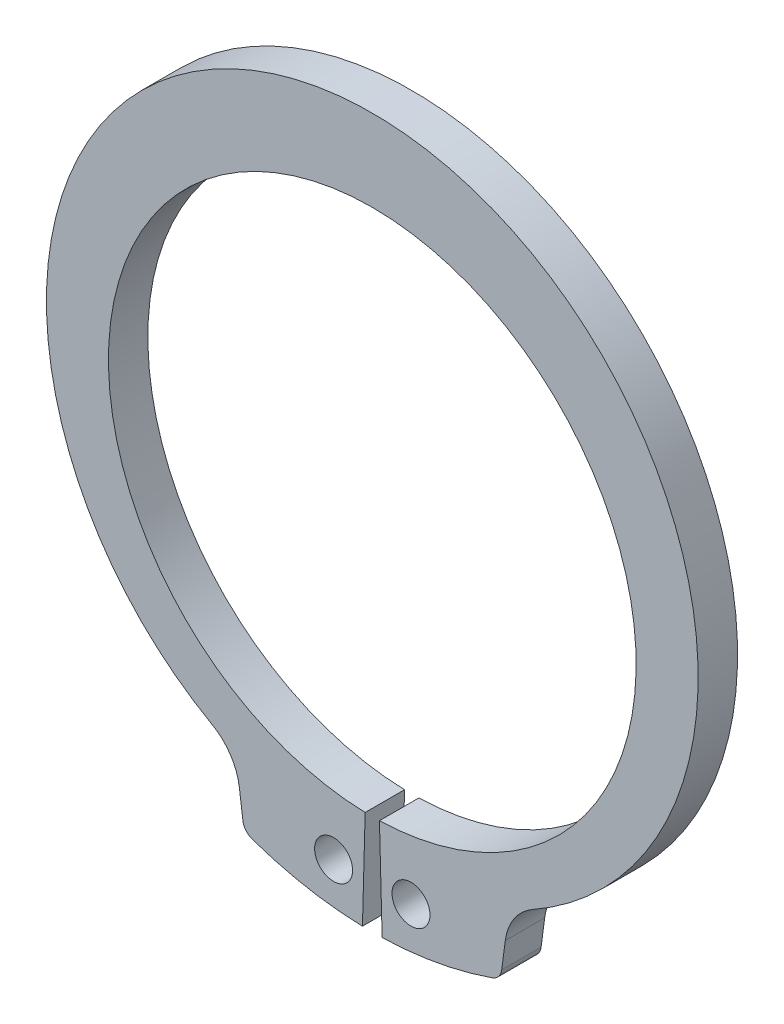
SolidWorks part; units mm, degrees
ref_plane "Plane1" through (0, 0, 0) normal (0, 0, 1) x (1, 0, 0)
ref_plane "Plane2" through (0, 0, 0) normal (0, 1, 0) x (1, 0, 0)
ref_plane "Plane3" through (0, 0, 0) normal (1, 0, 0) x (0, 0, -1)
sketch "Clipboard" plane through (0, 0, 0) normal (0, 0, 1) x (1, 0, 0)
  line L0 (0, 0) -> (5.8, 0)
  line L1 (0, 0) -> (0, 3.2)
  line L2 (0, 0) -> (0, -7.1)
  circle A0 centre (0, 0) radius 1.35
  circle A1 centre (0, 0) radius 20
  dimension "HoleDia" = 2.7
  dimension "ShaftDia" = 40
  dimension "LargeSection" = 5.8
  dimension "SmallSection" = 3.2
  dimension "LugSection" = 7.1
sketch "BodySke" plane through (0, 0, 0) normal (0, 0, 1) x (1, 0, 0)
  line L0 (-1.5431, 0) -> (1.5431, 0) construction
  line L1 (0, 0) -> (0, 24.55) construction
  line L2 (0.5077, -18.7431) -> (0.7, -25.8405)
  line L3 (-0.5077, -18.7431) -> (-0.7, -25.8405)
  line L4 (0, 0) -> (13.3149, -22.157) construction
  line L5 (0, 0) -> (-13.3149, -22.157) construction
  line L7 (9.4499, -21.6482) -> (9.1946, -23.5875)
  line L8 (-9.4499, -21.6482) -> (-9.1946, -23.5875)
  circle A0 centre (0, 0) radius 18.75 construction
  arc A1 (0.5077, -18.7431) -> (-0.5077, -18.7431) centre (0, 0) ccw
  arc A2 (11.3061, -18.8142) -> (-11.3061, -18.8142) centre (0, 1.394) ccw construction
  arc A3 (0.7, -25.8405) -> (8.5332, -24.4009) centre (0, 0) ccw
  arc A4 (11.3963, -18.7635) -> (9.4499, -21.6482) centre (13.3149, -22.157) ccw
  arc A5 (-9.4499, -21.6482) -> (-11.3963, -18.7635) centre (-13.3149, -22.157) ccw
  arc A6 (-8.5332, -24.4009) -> (-0.7, -25.8405) centre (0, 0) ccw
  arc A7 (11.3963, -18.7635) -> (-11.3963, -18.7635) centre (0, 1.394) ccw
  arc A8 (-9.5565, -20.8381) -> (9.5565, -20.8381) centre (0, 0) ccw construction
  circle A9 centre (2.75, -22.7595) radius 1.35
  circle A10 centre (-2.75, -22.7595) radius 1.35
  arc A11 (9.1946, -23.5875) -> (8.5332, -24.4009) centre (8.2031, -23.457) cw
  arc A12 (-9.1946, -23.5875) -> (-8.5332, -24.4009) centre (-8.2031, -23.457) ccw
  point P28 (9.1153, -24.1895)
  point P31 (-9.1153, -24.1895)
  dimension "GrooveDia" = 37.5
  dimension "LugRad" = 25.85
  dimension "HoleOffsetRad" = 22.925
  dimension "HoleDia" = 2.7
  dimension "D3" = 1
  dimension "LargeRad" = 24.55
  dimension "SmallRad" = 21.95
  dimension "SmallAngle" = 62.006
  dimension "D2" = 15
  dimension "HoleSpacing" = 5.5
  dimension "Gap" = 1.4
extrude "Body" add sketch "BodySke" against normal blind 2.8
sketch "NotSke" plane through (0, 0, 0) normal (0, 0, 1) x (1, 0, 0)
  line L0 (2.75, -21.4095) -> (2.75, -24.1095)
  line L1 (2.75, -24.1095) -> (-2.75, -24.1095)
  line L2 (-2.75, -24.1095) -> (-2.75, -21.4095)
  line L3 (-2.75, -21.4095) -> (2.75, -21.4095)
  circle A0 centre (2.75, -22.7595) radius 1.35 construction
  circle A1 centre (-2.75, -22.7595) radius 1.35 construction
extrude "Notch" [suppressed] cut sketch "NotSke" against normal through all
equation "' \"ShaftDia@Clipboard\" = 10"
equation "' \"Thickness@Body\" = 0.9"
equation "' \"GrooveDia@BodySke\" = 9.4"
equation "' \"LugSection@Clipboard\" = 2.6"
equation "' \"LargeSection@Clipboard\" = 1.7"
equation "' \"SmallSection@Clipboard\" = 1.0"
equation "' \"HoleDia@Clipboard\" = 1.0"
equation "' \"ShaftDia@Clipboard\" = 30"
equation "' \"Thickness@Body\" = 2.4"
equation "' \"GrooveDia@BodySke\" = 28.2"
equation "' \"LugSection@Clipboard\" = 5.6"
equation "' \"LargeSection@Clipboard\" = 4.5"
equation "' \"SmallSection@Clipboard\" = 2.5"
equation "' \"HoleDia@Clipboard\" = 2.3"
equation "\"Gap@BodySke\" =  \"Thickness@Body\" / 2"
equation "\"LargeRad@BodySke\" =  \"GrooveDia@BodySke\" / 2 +  \"LargeSection@Clipboard\""
equation "\"SmallRad@BodySke\" =  \"GrooveDia@BodySke\" / 2 +  \"SmallSection@Clipboard\""
equation "\"LugRad@BodySke\" = \"GrooveDia@BodySke\" / 2 + \"LugSection@Clipboard\""
equation "\"HoleOffsetRad@BodySke\" = (  \"ShaftDia@Clipboard\" / 2 + \"LugRad@BodySke\" ) / 2"
equation "\"HoleSpacing@BodySke\" = \"Gap@BodySke\"  * 2 +  \"HoleDia@Clipboard\""
equation "\"HoleDia@BodySke\" =  \"HoleDia@Clipboard\""
equation "\"SmallAngle@BodySke\" = atn(\"HoleSpacing@BodySke\" / 2 / sqr(\"HoleOffsetRad@BodySke\"  * \"HoleOffsetRad@BodySke\" - (\"HoleSpacing@BodySke\" / 2) * (\"HoleSpacing@BodySke\" / 2) ))  * 9 * ( 180 / 3.141593)"
